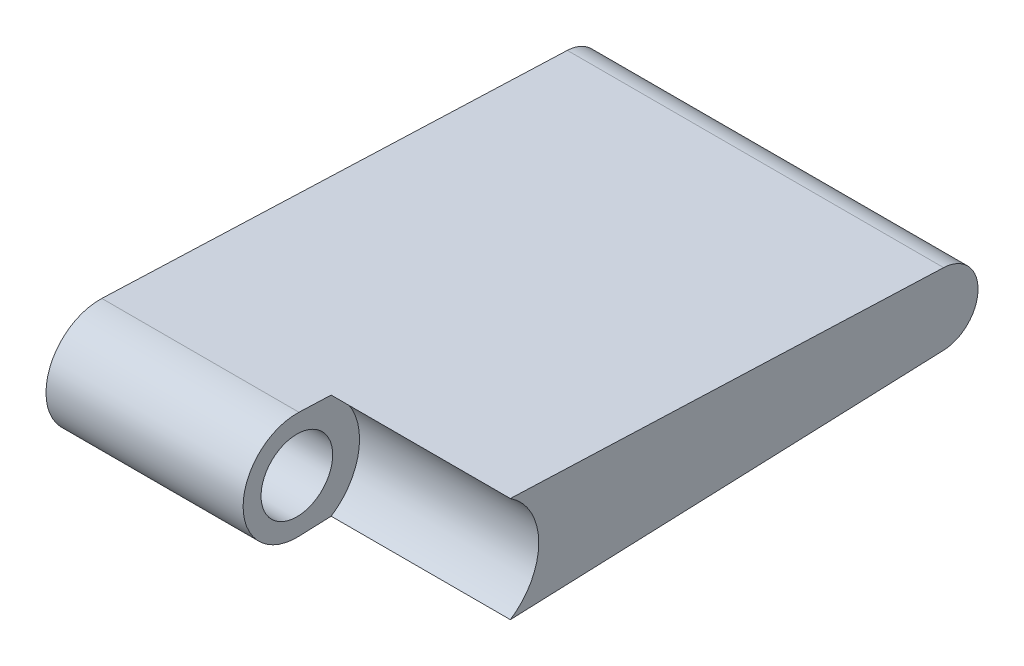
SolidWorks part; units mm, degrees
material "AISI 1035 Steel (SS)"
ref_plane "Front Plane" through (0, 0, 0) normal (0, 0, 1) x (1, 0, 0)
ref_plane "Top Plane" through (0, 0, 0) normal (0, 1, 0) x (1, 0, 0)
ref_plane "Right Plane" through (0, 0, 0) normal (1, 0, 0) x (0, 0, -1)
sketch "Sketch1" plane through (0, 0, 0) normal (1, 0, 0) x (0, 0, -1)
  line L0 (-10.1362, 2.3503) -> (10.2349, 1.566)
  line L1 (-10.1362, -2.3503) -> (10.2349, -1.566)
  arc A0 (10.2349, -1.566) -> (10.2349, 1.566) centre (10.1746, 0) ccw
  arc A1 (-10.1362, 2.3503) -> (-10.1362, -2.3503) centre (-10.2266, 0) ccw
  dimension "D1" = 20.4013
extrude "Boss-Extrude1" add sketch "Sketch1" against normal blind 16.4668
sketch "Sketch2" plane through (0, 0, 0) normal (1, 0, 0) x (0, 0, -1)
  circle A0 centre (-10.2266, 0) radius 2.7432
extrude "Cut-Extrude1" cut sketch "Sketch2" against normal blind 7.841
sketch "Sketch3" plane through (-7.841, 0, 0) normal (1, 0, 0) x (0, 0, -1)
  circle A0 centre (-10.2266, 0) radius 1.5672
extrude "Cut-Extrude2" cut sketch "Sketch3" against normal through all
